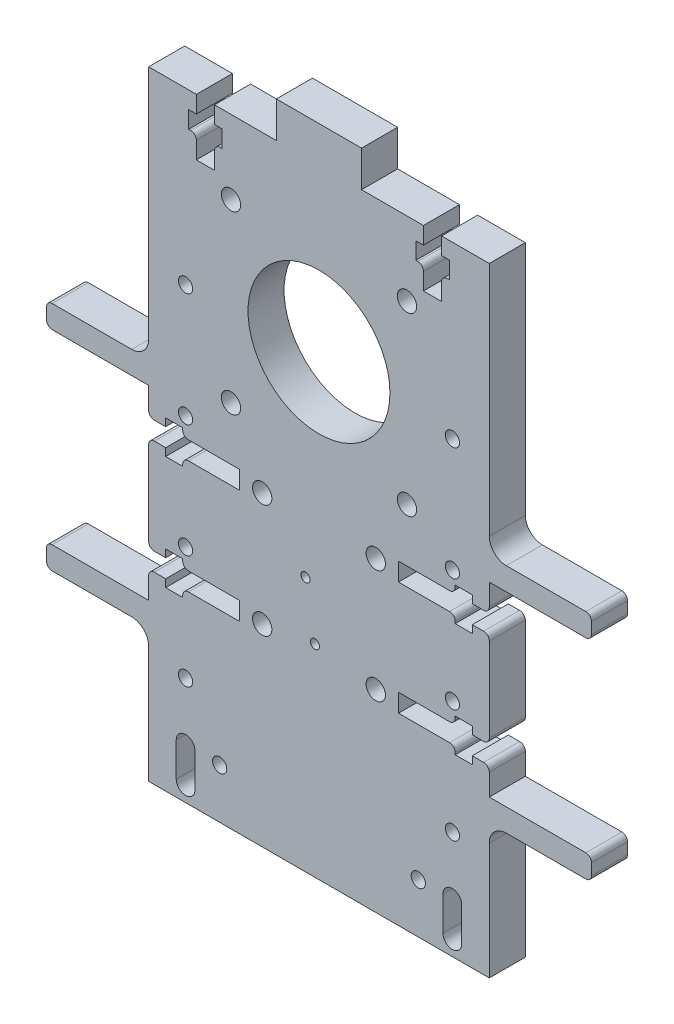
SolidWorks part; units mm, degrees
ref_plane "Front" through (0, 0, 0) normal (0, 0, 1) x (1, 0, 0)
ref_plane "Top" through (0, 0, 0) normal (0, 1, 0) x (1, 0, 0)
ref_plane "Right" through (0, 0, 0) normal (1, 0, 0) x (0, 0, -1)
ref_plane "Plane1" through (0, 0, 6.35) normal (0, 0, 1) x (1, 0, 0)
sketch "Sketch1" plane through (0, 0, 6.35) normal (0, 0, 1) x (1, 0, 0)
  line L0 (48, -56.9) -> (48, -52.9)
  line L1 (48, -52.9) -> (30, -52.9)
  line L2 (30, -52.9) -> (30, -48.1)
  line L3 (30, -48.1) -> (27, -48.1)
  line L4 (27, -48.1) -> (27, -49.45)
  line L5 (27, -49.45) -> (24, -49.45)
  line L6 (24, -49.45) -> (24, -48.1)
  line L7 (24, -48.1) -> (14, -48.1)
  line L8 (14, -48.1) -> (14, -44.9)
  line L9 (14, -44.9) -> (24, -44.9)
  line L10 (24, -44.9) -> (24, -43.55)
  line L11 (24, -43.55) -> (27, -43.55)
  line L12 (27, -43.55) -> (27, -44.9)
  line L13 (27, -44.9) -> (30, -44.9)
  line L14 (30, -44.9) -> (30, -28.1)
  line L15 (30, -28.1) -> (27, -28.1)
  line L16 (27, -28.1) -> (27, -29.45)
  line L17 (27, -29.45) -> (24, -29.45)
  line L18 (24, -29.45) -> (24, -28.1)
  line L19 (24, -28.1) -> (14, -28.1)
  line L20 (14, -28.1) -> (14, -24.9)
  line L21 (14, -24.9) -> (24, -24.9)
  line L22 (24, -24.9) -> (24, -23.55)
  line L23 (24, -23.55) -> (27, -23.55)
  line L24 (27, -23.55) -> (27, -24.9)
  line L25 (27, -24.9) -> (30, -24.9)
  line L26 (30, -24.9) -> (30, -20.1)
  line L27 (30, -20.1) -> (48, -20.1)
  line L28 (48, -20.1) -> (48, -16.1)
  line L29 (48, -16.1) -> (30, -16.1)
  line L30 (30, -16.1) -> (30, 28.5)
  line L31 (30, 28.5) -> (21.6, 28.5)
  line L32 (21.6, 28.5) -> (21.6, 25.5)
  line L33 (21.6, 25.5) -> (22.95, 25.5)
  line L34 (22.95, 25.5) -> (22.95, 22.5)
  line L35 (22.95, 22.5) -> (21.6, 22.5)
  line L36 (21.6, 22.5) -> (21.6, 18.5)
  line L37 (21.6, 18.5) -> (18.4, 18.5)
  line L38 (18.4, 18.5) -> (18.4, 22.5)
  line L39 (18.4, 22.5) -> (17.05, 22.5)
  line L40 (17.05, 22.5) -> (17.05, 25.5)
  line L41 (17.05, 25.5) -> (18.4, 25.5)
  line L42 (18.4, 25.5) -> (18.4, 28.5)
  line L43 (18.4, 28.5) -> (7.5, 28.5)
  line L44 (7.5, 28.5) -> (7.5, 34.85)
  line L45 (7.5, 34.85) -> (-7.5, 34.85)
  line L46 (-7.5, 34.85) -> (-7.5, 28.5)
  line L47 (-7.5, 28.5) -> (-18.4, 28.5)
  line L48 (-18.4, 28.5) -> (-18.4, 25.5)
  line L49 (-18.4, 25.5) -> (-17.05, 25.5)
  line L50 (-17.05, 25.5) -> (-17.05, 22.5)
  line L51 (-17.05, 22.5) -> (-18.4, 22.5)
  line L52 (-18.4, 22.5) -> (-18.4, 18.5)
  line L53 (-18.4, 18.5) -> (-21.6, 18.5)
  line L54 (-21.6, 18.5) -> (-21.6, 22.5)
  line L55 (-21.6, 22.5) -> (-22.95, 22.5)
  line L56 (-22.95, 22.5) -> (-22.95, 25.5)
  line L57 (-22.95, 25.5) -> (-21.6, 25.5)
  line L58 (-21.6, 25.5) -> (-21.6, 28.5)
  line L59 (-21.6, 28.5) -> (-30, 28.5)
  line L60 (-30, 28.5) -> (-30, -16.1)
  line L61 (-30, -16.1) -> (-48, -16.1)
  line L62 (-48, -16.1) -> (-48, -20.1)
  line L63 (-48, -20.1) -> (-30, -20.1)
  line L64 (-30, -20.1) -> (-30, -24.9)
  line L65 (-30, -24.9) -> (-27, -24.9)
  line L66 (-27, -24.9) -> (-27, -23.55)
  line L67 (-27, -23.55) -> (-24, -23.55)
  line L68 (-24, -23.55) -> (-24, -24.9)
  line L69 (-24, -24.9) -> (-14, -24.9)
  line L70 (-14, -24.9) -> (-14, -28.1)
  line L71 (-14, -28.1) -> (-24, -28.1)
  line L72 (-24, -28.1) -> (-24, -29.45)
  line L73 (-24, -29.45) -> (-27, -29.45)
  line L74 (-27, -29.45) -> (-27, -28.1)
  line L75 (-27, -28.1) -> (-30, -28.1)
  line L76 (-30, -28.1) -> (-30, -44.9)
  line L77 (-30, -44.9) -> (-27, -44.9)
  line L78 (-27, -44.9) -> (-27, -43.55)
  line L79 (-27, -43.55) -> (-24, -43.55)
  line L80 (-24, -43.55) -> (-24, -44.9)
  line L81 (-24, -44.9) -> (-14, -44.9)
  line L82 (-14, -44.9) -> (-14, -48.1)
  line L83 (-14, -48.1) -> (-24, -48.1)
  line L84 (-24, -48.1) -> (-24, -49.45)
  line L85 (-24, -49.45) -> (-27, -49.45)
  line L86 (-27, -49.45) -> (-27, -48.1)
  line L87 (-27, -48.1) -> (-30, -48.1)
  line L88 (-30, -48.1) -> (-30, -52.9)
  line L89 (-30, -52.9) -> (-48, -52.9)
  line L90 (-48, -52.9) -> (-48, -56.9)
  line L91 (-48, -56.9) -> (-30, -56.9)
  line L92 (-30, -56.9) -> (-30, -80.5)
  line L93 (-30, -80.5) -> (30, -80.5)
  line L94 (30, -80.5) -> (30, -56.9)
  line L95 (30, -56.9) -> (48, -56.9)
  line L96 (-21.8424, -71.75) -> (-21.8424, -77.75)
  line L97 (-25.1424, -77.75) -> (-25.1424, -71.75)
  line L98 (21.8424, -77.75) -> (21.8424, -71.75)
  line L99 (25.1424, -71.75) -> (25.1424, -77.75)
  arc A0 (-25.1424, -71.75) -> (-21.8424, -71.75) centre (-23.4924, -71.75) cw
  arc A1 (-21.8424, -77.75) -> (-25.1424, -77.75) centre (-23.4924, -77.75) cw
  arc A2 (25.1424, -77.75) -> (21.8424, -77.75) centre (23.4924, -77.75) cw
  arc A3 (21.8424, -71.75) -> (25.1424, -71.75) centre (23.4924, -71.75) cw
extrude "Boss-Extrude1" add sketch "Sketch1" against normal blind 6.35
fillet "Fillet1" radius 1 24 edges at (-48, -16.1, 3.175) (48, -16.1, 3.175) (48, -56.9, 3.175) (30, -24.9, 3.175) (-30, -44.9, 3.175) (30, -28.1, 3.175) (-30, -24.9, 3.175) (30, -44.9, 3.175) (-30, -48.1, 3.175) (30, -48.1, 3.175) (-30, -28.1, 3.175) (-24, -48.1, 3.175) (-24, -44.9, 3.175) (-24, -28.1, 3.175) (-24, -24.9, 3.175) (24, -28.1, 3.175) (24, -24.9, 3.175) (24, -48.1, 3.175) (24, -44.9, 3.175) (48, -52.9, 3.175) (48, -20.1, 3.175) (-48, -56.9, 3.175) (-48, -52.9, 3.175) (-48, -20.1, 3.175)
fillet "Fillet3" radius 3 4 edges at (-30, -16.1, 3.175) (30, -16.1, 3.175) (-30, -56.9, 3.175) (30, -56.9, 3.175)
hole_wizard "M2 Tapped Hole1" positions "Sketch3" profile "Sketch2" tap size "M2" standard "ISO" end condition through all
sketch "Sketch3" plane through (0, 0, 6.35) normal (0, 0, 1) x (1, 0, 0)
  point P0 (-2.3593, -35.5451)
sketch "Sketch2" plane through (-2.3593, -35.5451, 6.35) normal (1, 0, 0) x (0, -1, 0)
  line L0 (0, 0) -> (0, 6.35)
  line L1 (0, 6.35) -> (0.8, 6.35)
  line L2 (0.8, 6.35) -> (0.8, 0)
  line L5 (0.8, 0) -> (0, 0)
  line L11 (0, -6.35) -> (0, 107.95) construction
  dimension "Thru Tap Drill Dia." = 1.6
  dimension "Thru Tap Drill Depth" = 6.35
cosmetic thread "Hole Thread11" parameters "D2"=2
hole_wizard "M2 Tapped Hole2" positions "Sketch5" profile "Sketch4" tap size "M2" standard "ISO" end condition through all
sketch "Sketch5" plane through (0, 0, 6.35) normal (0, 0, 1) x (1, 0, 0)
  point P0 (-0.7096, -44.9008)
sketch "Sketch4" plane through (-0.7096, -44.9008, 6.35) normal (1, 0, 0) x (0, -1, 0)
  line L0 (0, 0) -> (0, 6.35)
  line L1 (0, 6.35) -> (0.8, 6.35)
  line L2 (0.8, 6.35) -> (0.8, 0)
  line L5 (0.8, 0) -> (0, 0)
  line L11 (0, -6.35) -> (0, 107.95) construction
  dimension "Thru Tap Drill Dia." = 1.6
  dimension "Thru Tap Drill Depth" = 6.35
cosmetic thread "Hole Thread12" parameters "D2"=2
hole_wizard "M3 Clearance Hole1" positions "Sketch7" profile "Sketch6" hole size "M3" standard "ISO" end condition through all
sketch "Sketch7" plane through (0, 0, 6.35) normal (0, 0, 1) x (1, 0, 0)
  point P0 (15.5, 15.5)
sketch "Sketch6" plane through (15.5, 15.5, 6.35) normal (1, 0, 0) x (0, -1, 0)
  line L0 (0, 0) -> (0, 6.35)
  line L1 (0, 6.35) -> (1.7, 6.35)
  line L2 (1.7, 6.35) -> (1.7, 0)
  line L5 (1.7, 0) -> (0, 0)
  line L11 (0, -6.35) -> (0, 107.95) construction
  dimension "Thru Hole Dia." = 3.4
  dimension "Thru Hole Depth" = 6.35
hole_wizard "M3 Clearance Hole2" positions "Sketch9" profile "Sketch8" hole size "M3" standard "ISO" end condition through all
sketch "Sketch9" plane through (0, 0, 6.35) normal (0, 0, 1) x (1, 0, 0)
  point P0 (-15.5, -15.5)
sketch "Sketch8" plane through (-15.5, -15.5, 6.35) normal (1, 0, 0) x (0, -1, 0)
  line L0 (0, 0) -> (0, 6.35)
  line L1 (0, 6.35) -> (1.7, 6.35)
  line L2 (1.7, 6.35) -> (1.7, 0)
  line L5 (1.7, 0) -> (0, 0)
  line L11 (0, -6.35) -> (0, 107.95) construction
  dimension "Thru Hole Dia." = 3.4
  dimension "Thru Hole Depth" = 6.35
hole_wizard "M3 Clearance Hole3" positions "Sketch11" profile "Sketch10" hole size "M3" standard "ISO" end condition through all
sketch "Sketch11" plane through (0, 0, 6.35) normal (0, 0, 1) x (1, 0, 0)
  point P0 (15.5, -15.5)
sketch "Sketch10" plane through (15.5, -15.5, 6.35) normal (1, 0, 0) x (0, -1, 0)
  line L0 (0, 0) -> (0, 6.35)
  line L1 (0, 6.35) -> (1.7, 6.35)
  line L2 (1.7, 6.35) -> (1.7, 0)
  line L5 (1.7, 0) -> (0, 0)
  line L11 (0, -6.35) -> (0, 107.95) construction
  dimension "Thru Hole Dia." = 3.4
  dimension "Thru Hole Depth" = 6.35
hole_wizard "M3 Clearance Hole4" positions "Sketch13" profile "Sketch12" hole size "M3" standard "ISO" end condition through all
sketch "Sketch13" plane through (0, 0, 6.35) normal (0, 0, 1) x (1, 0, 0)
  point P0 (-15.5, 15.5)
sketch "Sketch12" plane through (-15.5, 15.5, 6.35) normal (1, 0, 0) x (0, -1, 0)
  line L0 (0, 0) -> (0, 6.35)
  line L1 (0, 6.35) -> (1.7, 6.35)
  line L2 (1.7, 6.35) -> (1.7, 0)
  line L5 (1.7, 0) -> (0, 0)
  line L11 (0, -6.35) -> (0, 107.95) construction
  dimension "Thru Hole Dia." = 3.4
  dimension "Thru Hole Depth" = 6.35
hole_wizard "M3 Tapped Hole2" positions "Sketch15" profile "Sketch14" tap size "M3" standard "ISO" end condition through all
sketch "Sketch15" plane through (0, 0, 6.35) normal (0, 0, 1) x (1, 0, 0)
  point P0 (23.5, -61.5)
sketch "Sketch14" plane through (23.5, -61.5, 6.35) normal (1, 0, 0) x (0, -1, 0)
  line L0 (0, 0) -> (0, 6.35)
  line L1 (0, 6.35) -> (1.25, 6.35)
  line L2 (1.25, 6.35) -> (1.25, 0)
  line L5 (1.25, 0) -> (0, 0)
  line L11 (0, -6.35) -> (0, 107.95) construction
  dimension "Thru Tap Drill Dia." = 2.5
  dimension "Thru Tap Drill Depth" = 6.35
cosmetic thread "Hole Thread1" parameters "D2"=3
hole_wizard "M3 Tapped Hole3" positions "Sketch17" profile "Sketch16" tap size "M3" standard "ISO" end condition through all
sketch "Sketch17" plane through (0, 0, 6.35) normal (0, 0, 1) x (1, 0, 0)
  point P0 (23.5, -41.5)
sketch "Sketch16" plane through (23.5, -41.5, 6.35) normal (1, 0, 0) x (0, -1, 0)
  line L0 (0, 0) -> (0, 6.35)
  line L1 (0, 6.35) -> (1.25, 6.35)
  line L2 (1.25, 6.35) -> (1.25, 0)
  line L5 (1.25, 0) -> (0, 0)
  line L11 (0, -6.35) -> (0, 107.95) construction
  dimension "Thru Tap Drill Dia." = 2.5
  dimension "Thru Tap Drill Depth" = 6.35
cosmetic thread "Hole Thread3" parameters "D2"=3
hole_wizard "M3 Tapped Hole4" positions "Sketch19" profile "Sketch18" tap size "M3" standard "ISO" end condition through all
sketch "Sketch19" plane through (0, 0, 6.35) normal (0, 0, 1) x (1, 0, 0)
  point P0 (23.5, -21.5)
sketch "Sketch18" plane through (23.5, -21.5, 6.35) normal (1, 0, 0) x (0, -1, 0)
  line L0 (0, 0) -> (0, 6.35)
  line L1 (0, 6.35) -> (1.25, 6.35)
  line L2 (1.25, 6.35) -> (1.25, 0)
  line L5 (1.25, 0) -> (0, 0)
  line L11 (0, -6.35) -> (0, 107.95) construction
  dimension "Thru Tap Drill Dia." = 2.5
  dimension "Thru Tap Drill Depth" = 6.35
cosmetic thread "Hole Thread4" parameters "D2"=3
hole_wizard "M3 Tapped Hole5" positions "Sketch21" profile "Sketch20" tap size "M3" standard "ISO" end condition through all
sketch "Sketch21" plane through (0, 0, 6.35) normal (0, 0, 1) x (1, 0, 0)
  point P0 (23.5, -1.5)
sketch "Sketch20" plane through (23.5, -1.5, 6.35) normal (1, 0, 0) x (0, -1, 0)
  line L0 (0, 0) -> (0, 6.35)
  line L1 (0, 6.35) -> (1.25, 6.35)
  line L2 (1.25, 6.35) -> (1.25, 0)
  line L5 (1.25, 0) -> (0, 0)
  line L11 (0, -6.35) -> (0, 107.95) construction
  dimension "Thru Tap Drill Dia." = 2.5
  dimension "Thru Tap Drill Depth" = 6.35
cosmetic thread "Hole Thread5" parameters "D2"=3
hole_wizard "M3 Tapped Hole6" positions "Sketch23" profile "Sketch22" tap size "M3" standard "ISO" end condition through all
sketch "Sketch23" plane through (0, 0, 6.35) normal (0, 0, 1) x (1, 0, 0)
  point P0 (-17.4924, -71.75)
sketch "Sketch22" plane through (-17.4924, -71.75, 6.35) normal (1, 0, 0) x (0, -1, 0)
  line L0 (0, 0) -> (0, 6.35)
  line L1 (0, 6.35) -> (1.25, 6.35)
  line L2 (1.25, 6.35) -> (1.25, 0)
  line L5 (1.25, 0) -> (0, 0)
  line L11 (0, -6.35) -> (0, 107.95) construction
  dimension "Thru Tap Drill Dia." = 2.5
  dimension "Thru Tap Drill Depth" = 6.35
cosmetic thread "Hole Thread6" parameters "D2"=3
hole_wizard "M3 Tapped Hole7" positions "Sketch25" profile "Sketch24" tap size "M3" standard "ISO" end condition through all
sketch "Sketch25" plane through (0, 0, 6.35) normal (0, 0, 1) x (1, 0, 0)
  point P0 (17.4924, -71.75)
sketch "Sketch24" plane through (17.4924, -71.75, 6.35) normal (1, 0, 0) x (0, -1, 0)
  line L0 (0, 0) -> (0, 6.35)
  line L1 (0, 6.35) -> (1.25, 6.35)
  line L2 (1.25, 6.35) -> (1.25, 0)
  line L5 (1.25, 0) -> (0, 0)
  line L11 (0, -6.35) -> (0, 107.95) construction
  dimension "Thru Tap Drill Dia." = 2.5
  dimension "Thru Tap Drill Depth" = 6.35
cosmetic thread "Hole Thread7" parameters "D2"=3
hole_wizard "M3 Tapped Hole8" positions "Sketch27" profile "Sketch26" tap size "M3" standard "ISO" end condition through all
sketch "Sketch27" plane through (0, 0, 6.35) normal (0, 0, 1) x (1, 0, 0)
  point P0 (-23.5, -41.5)
sketch "Sketch26" plane through (-23.5, -41.5, 6.35) normal (1, 0, 0) x (0, -1, 0)
  line L0 (0, 0) -> (0, 6.35)
  line L1 (0, 6.35) -> (1.25, 6.35)
  line L2 (1.25, 6.35) -> (1.25, 0)
  line L5 (1.25, 0) -> (0, 0)
  line L11 (0, -6.35) -> (0, 107.95) construction
  dimension "Thru Tap Drill Dia." = 2.5
  dimension "Thru Tap Drill Depth" = 6.35
cosmetic thread "Hole Thread8" parameters "D2"=3
hole_wizard "M3 Tapped Hole9" positions "Sketch29" profile "Sketch28" tap size "M3" standard "ISO" end condition through all
sketch "Sketch29" plane through (0, 0, 6.35) normal (0, 0, 1) x (1, 0, 0)
  point P0 (-23.5, -61.5)
sketch "Sketch28" plane through (-23.5, -61.5, 6.35) normal (1, 0, 0) x (0, -1, 0)
  line L0 (0, 0) -> (0, 6.35)
  line L1 (0, 6.35) -> (1.25, 6.35)
  line L2 (1.25, 6.35) -> (1.25, 0)
  line L5 (1.25, 0) -> (0, 0)
  line L11 (0, -6.35) -> (0, 107.95) construction
  dimension "Thru Tap Drill Dia." = 2.5
  dimension "Thru Tap Drill Depth" = 6.35
cosmetic thread "Hole Thread9" parameters "D2"=3
hole_wizard "M3 Tapped Hole10" positions "Sketch31" profile "Sketch30" tap size "M3" standard "ISO" end condition through all
sketch "Sketch31" plane through (0, 0, 6.35) normal (0, 0, 1) x (1, 0, 0)
  point P0 (-23.5, -21.5)
sketch "Sketch30" plane through (-23.5, -21.5, 6.35) normal (1, 0, 0) x (0, -1, 0)
  line L0 (0, 0) -> (0, 6.35)
  line L1 (0, 6.35) -> (1.25, 6.35)
  line L2 (1.25, 6.35) -> (1.25, 0)
  line L5 (1.25, 0) -> (0, 0)
  line L11 (0, -6.35) -> (0, 107.95) construction
  dimension "Thru Tap Drill Dia." = 2.5
  dimension "Thru Tap Drill Depth" = 6.35
cosmetic thread "Hole Thread10" parameters "D2"=3
hole_wizard "M3 Clearance Hole8" positions "Sketch33" profile "Sketch32" hole size "M3" standard "ISO" end condition through all
sketch "Sketch33" plane through (0, 0, 6.35) normal (0, 0, 1) x (1, 0, 0)
  point P0 (-10, -46.5)
sketch "Sketch32" plane through (-10, -46.5, 6.35) normal (1, 0, 0) x (0, -1, 0)
  line L0 (0, 0) -> (0, 6.35)
  line L1 (0, 6.35) -> (1.7, 6.35)
  line L2 (1.7, 6.35) -> (1.7, 0)
  line L5 (1.7, 0) -> (0, 0)
  line L11 (0, -6.35) -> (0, 107.95) construction
  dimension "Thru Hole Dia." = 3.4
  dimension "Thru Hole Depth" = 6.35
hole_wizard "M3 Clearance Hole7" positions "Sketch35" profile "Sketch34" hole size "M3" standard "ISO" end condition through all
sketch "Sketch35" plane through (0, 0, 6.35) normal (0, 0, 1) x (1, 0, 0)
  point P0 (10, -46.5)
sketch "Sketch34" plane through (10, -46.5, 6.35) normal (1, 0, 0) x (0, -1, 0)
  line L0 (0, 0) -> (0, 6.35)
  line L1 (0, 6.35) -> (1.7, 6.35)
  line L2 (1.7, 6.35) -> (1.7, 0)
  line L5 (1.7, 0) -> (0, 0)
  line L11 (0, -6.35) -> (0, 107.95) construction
  dimension "Thru Hole Dia." = 3.4
  dimension "Thru Hole Depth" = 6.35
hole_wizard "M3 Tapped Hole1" positions "Sketch37" profile "Sketch36" tap size "M3" standard "ISO" end condition through all
sketch "Sketch37" plane through (0, 0, 6.35) normal (0, 0, 1) x (1, 0, 0)
  point P0 (-23.5, -1.5)
sketch "Sketch36" plane through (-23.5, -1.5, 6.35) normal (1, 0, 0) x (0, -1, 0)
  line L0 (0, 0) -> (0, 6.35)
  line L1 (0, 6.35) -> (1.25, 6.35)
  line L2 (1.25, 6.35) -> (1.25, 0)
  line L5 (1.25, 0) -> (0, 0)
  line L11 (0, -6.35) -> (0, 107.95) construction
  dimension "Thru Tap Drill Dia." = 2.5
  dimension "Thru Tap Drill Depth" = 6.35
cosmetic thread "Hole Thread2" parameters "D2"=3
hole_wizard "M3 Clearance Hole6" positions "Sketch39" profile "Sketch38" hole size "M3" standard "ISO" end condition through all
sketch "Sketch39" plane through (0, 0, 6.35) normal (0, 0, 1) x (1, 0, 0)
  point P0 (10, -26.5)
sketch "Sketch38" plane through (10, -26.5, 6.35) normal (1, 0, 0) x (0, -1, 0)
  line L0 (0, 0) -> (0, 6.35)
  line L1 (0, 6.35) -> (1.7, 6.35)
  line L2 (1.7, 6.35) -> (1.7, 0)
  line L5 (1.7, 0) -> (0, 0)
  line L11 (0, -6.35) -> (0, 107.95) construction
  dimension "Thru Hole Dia." = 3.4
  dimension "Thru Hole Depth" = 6.35
hole_wizard "Ø25.0 (25) Diameter Hole1" positions "Sketch41" profile "Sketch40" hole size "Ø25.0" standard "ANSI Metric"
sketch "Sketch41" plane through (0, 0, 6.35) normal (0, 0, 1) x (1, 0, 0)
  point P0 (0, 0)
sketch "Sketch40" plane through (0, 0, 6.35) normal (1, 0, 0) x (0, -1, 0)
  line L0 (0, 0) -> (0, 6.35)
  line L1 (0, 6.35) -> (12.5, 6.35)
  line L2 (12.5, 6.35) -> (12.5, 0)
  line L5 (12.5, 0) -> (0, 0)
  line L11 (0, -6.35) -> (0, 107.95) construction
  dimension "Thru Hole Dia." = 25
  dimension "Thru Hole Depth" = 6.35
hole_wizard "M3 Clearance Hole5" positions "Sketch43" profile "Sketch42" hole size "M3" standard "ISO" end condition through all
sketch "Sketch43" plane through (0, 0, 6.35) normal (0, 0, 1) x (1, 0, 0)
  point P0 (-10, -26.5)
sketch "Sketch42" plane through (-10, -26.5, 6.35) normal (1, 0, 0) x (0, -1, 0)
  line L0 (0, 0) -> (0, 6.35)
  line L1 (0, 6.35) -> (1.7, 6.35)
  line L2 (1.7, 6.35) -> (1.7, 0)
  line L5 (1.7, 0) -> (0, 0)
  line L11 (0, -6.35) -> (0, 107.95) construction
  dimension "Thru Hole Dia." = 3.4
  dimension "Thru Hole Depth" = 6.35
fillet "Fillet4" radius 1 4 edges at (21.6, 22.5, 3.175) (18.4, 22.5, 3.175) (-18.4, 22.5, 3.175) (-21.6, 22.5, 3.175)
